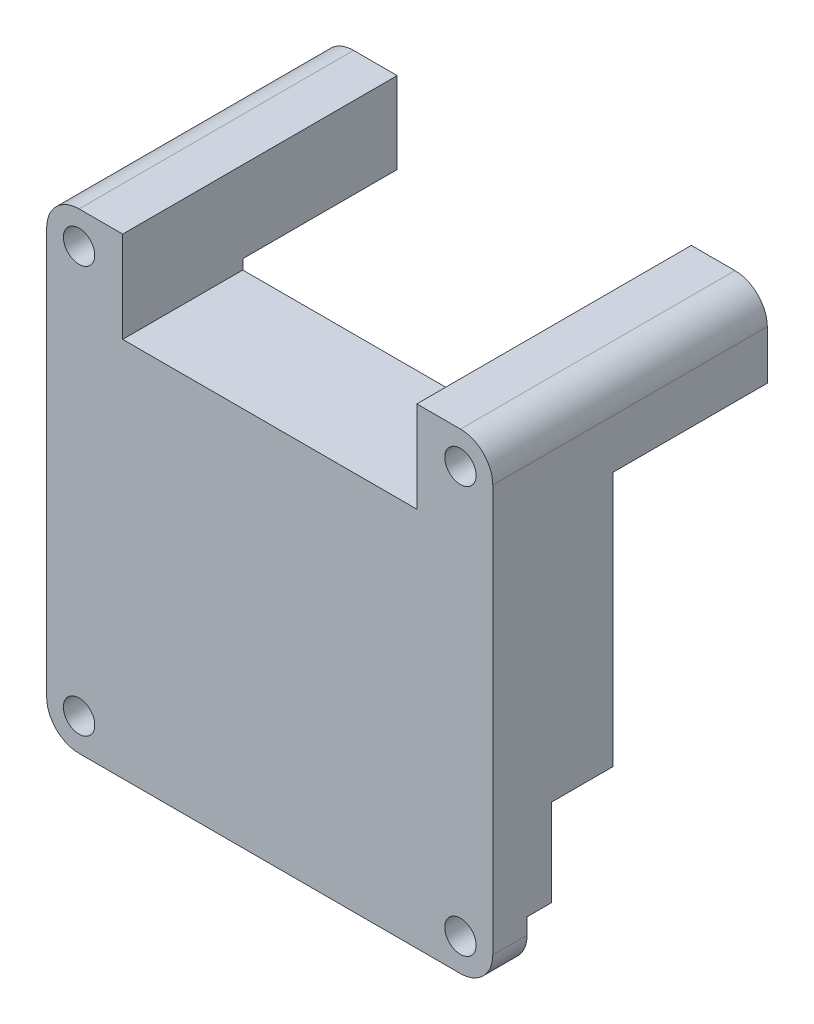
SolidWorks part; units mm, degrees
ref_plane "Přední rovina" through (0, 0, 0) normal (0, 0, 1) x (1, 0, 0)
ref_plane "Horní rovina" through (0, 0, 0) normal (0, 1, 0) x (1, 0, 0)
ref_plane "Pravá rovina" through (0, 0, 0) normal (1, 0, 0) x (0, 0, -1)
sketch "Skica1" plane through (0, 0, 0) normal (0, 0, 1) x (1, 0, 0)
  line L1 (19.45, -3.3) -> (-19.45, -3.3)
  line L2 (22.75, 41.5) -> (22.75, 0)
  line L3 (19.45, 44.8) -> (-19.45, 44.8)
  line L4 (-22.75, 41.5) -> (-22.75, 0)
  circle A0 centre (19.45, 0) radius 1.6
  circle A1 centre (-19.45, 0) radius 1.6
  arc A2 (-22.75, 0) -> (-19.45, -3.3) centre (-19.45, 0) ccw
  arc A3 (19.45, -3.3) -> (22.75, 0) centre (19.45, 0) ccw
  circle A4 centre (19.45, 41.5) radius 1.6
  circle A5 centre (-19.45, 41.5) radius 1.6
  arc A6 (22.75, 41.5) -> (19.45, 44.8) centre (19.45, 41.5) ccw
  arc A7 (-19.45, 44.8) -> (-22.75, 41.5) centre (-19.45, 41.5) ccw
  dimension "D1" = 3.2
  dimension "D2" = 3.2
  dimension "D5" = 6.6
  dimension "D6" = 6.6
  dimension "D8" = 6.6
  dimension "D9" = 6.6
  dimension "D10" = 3.2
  dimension "D11" = 3.2
  dimension "D3" = 19.45
  dimension "D4" = 19.45
  dimension "D7" = 41.5
extrude "Přidat vysunutím1" add sketch "Skica1" along normal blind 28
sketch "Skica5" plane through (0, 0, 0) normal (0, 0, 1) x (1, 0, 0)
  line L0 (-19.45, -3.3) -> (19.45, -3.3) construction
  line L1 (16.5, 24.6) -> (-16.5, 24.6)
  line L2 (16.5, 24.6) -> (16.5, -4.3)
  line L3 (16.5, -4.3) -> (-16.5, -4.3)
  line L4 (-16.5, 24.6) -> (-16.5, -4.3)
  point P6 (0, -4.3)
  point P7 (0, -3.3)
  dimension "D1" = 1
  dimension "D2" = 28.9
  dimension "D3" = 33
extrude "Odebrat vysunutím3" cut sketch "Skica5" along normal blind 22
sketch "Skica7" plane through (0, 0, 0) normal (0, 0, 1) x (1, 0, 0)
  line L0 (19.45, 44.8) -> (-19.45, 44.8) construction
  line L1 (-15, 45.8) -> (15, 45.8)
  line L2 (-15, 45.8) -> (-15, 35.5)
  line L3 (-15, 35.5) -> (15, 35.5)
  line L4 (15, 45.8) -> (15, 35.5)
  line L5 (16.5, -3.3) -> (-16.5, -3.3) construction
  point P6 (0, -3.3)
  point P9 (0, 35.5)
  dimension "D1" = 10.3
  dimension "D2" = 1
  dimension "D3" = 30
  dimension "D4" = 0
extrude "Odebrat vysunutím5" cut sketch "Skica7" along normal through all
sketch "Skica6" plane through (0, 0, 0) normal (0, 0, 1) x (1, 0, 0)
  line L1 (23.75, 36.5) -> (-23.75, 36.5)
  line L2 (23.75, 36.5) -> (23.75, 10.5)
  line L3 (23.75, 10.5) -> (-23.75, 10.5)
  line L4 (-23.75, 36.5) -> (-23.75, 10.5)
  line L5 (-22.75, 41.5) -> (-22.75, 0) construction
  line L6 (22.75, 0) -> (22.75, 41.5) construction
  line L7 (-15, 35.5) -> (15, 35.5) construction
  dimension "D1" = 1
  dimension "D2" = 1
  dimension "D3" = 1
  dimension "D4" = 26
extrude "Odebrat vysunutím4" cut sketch "Skica6" along normal blind 15.75
sketch "Skica8" plane through (0, 0, 0) normal (0, 0, 1) x (1, 0, 0)
  line L0 (16.5, -3.3) -> (-16.5, -3.3) construction
  line L1 (-25, 10.5) -> (25, 10.5)
  line L2 (-25, 10.5) -> (-25, -5.5)
  line L3 (-25, -5.5) -> (25, -5.5)
  line L4 (25, 10.5) -> (25, -5.5)
  line L5 (-22.75, 10.5) -> (-16.5, 10.5) construction
  point P4 (0, -5.5)
  point P7 (0, -3.3)
  dimension "D1" = 50
  dimension "D2" = 0
  dimension "D3" = 16
extrude "Odebrat vysunutím6" cut sketch "Skica8" along normal blind 22
ref_plane "Rovina3" through (0, 0, 22) normal (0, 0, 1) x (1, 0, 0)
sketch "Skica9" plane through (0, 0, 22) normal (0, 0, 1) x (1, 0, 0)
  line L0 (-19.45, -3.2332) -> (-19.45, -4.033)
  line L1 (-19.45, 3.2332) -> (-22.25, 1.6166)
  line L4 (-19.45, -3.2332) -> (-16.65, -1.6166)
  line L5 (-16.65, -1.6166) -> (-16.65, 1.6166)
  line L6 (-16.65, 1.6166) -> (-19.45, 3.2332)
  line L13 (-19.45, -4.033) -> (-23.9669, -4.033)
  line L14 (-23.9669, -4.033) -> (-23.9669, 1.6166)
  line L15 (-23.9669, 1.6166) -> (-22.25, 1.6166)
  line L17 (-22.25, 0) -> (-22.25, -1.6166) [skipped]
  line L18 (-22.25, -1.6166) -> (-20.85, -2.4249) [skipped]
  circle A0 centre (-19.45, 0) radius 2.8 construction
  dimension "D2" = 5.6
extrude "Odebrat vysunutím7" cut sketch "Skica9" along normal blind 2.5
mirror "Zrcadlit1" about plane through (0, 0, 0) normal (1, 0, 0) of "Odebrat vysunutím7"
